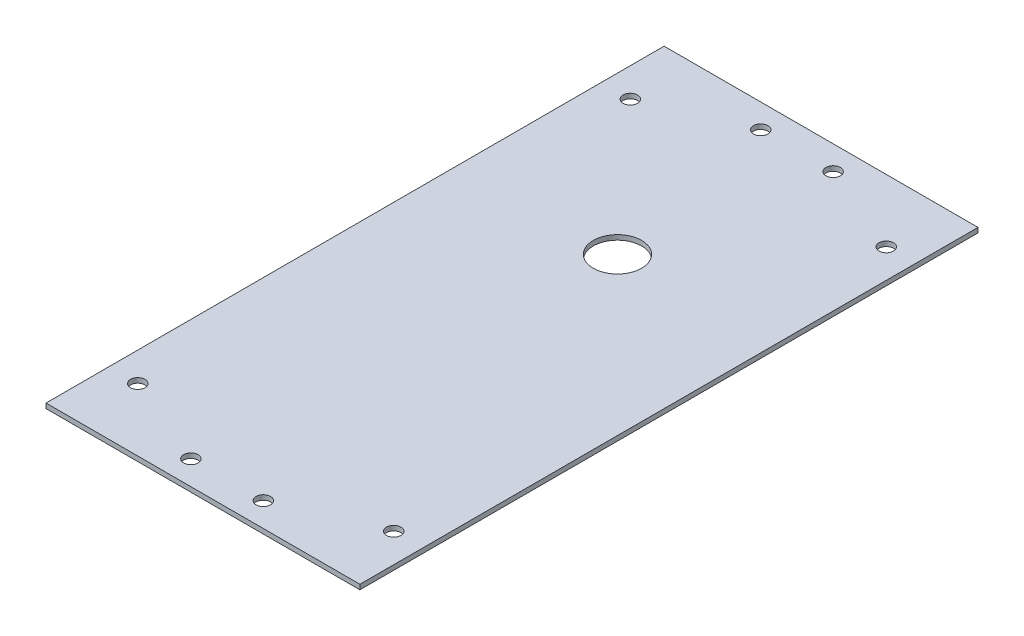
SolidWorks part; units mm, degrees
ref_plane "Спереди" through (0, 0, 0) normal (0, 0, 1) x (1, 0, 0)
ref_plane "Сверху" through (0, 0, 0) normal (0, 1, 0) x (1, 0, 0)
ref_plane "Справа" through (0, 0, 0) normal (1, 0, 0) x (0, 0, -1)
sketch "Эскиз1" plane through (0, 0, 0) normal (0, 1, 0) x (1, 0, 0)
  line L0 (-41.8585, 53.6415) -> (-41.8585, -74.3585) construction
  line L1 (-74.3585, 53.6415) -> (-9.3585, 53.6415)
  line L2 (-74.3585, 53.6415) -> (-74.3585, -74.3585)
  line L3 (-74.3585, -74.3585) -> (-9.3585, -74.3585)
  line L4 (-9.3585, 53.6415) -> (-9.3585, -74.3585)
  line L5 (-74.3585, -10.3585) -> (-9.3585, -10.3585) construction
  circle A0 centre (-68.3585, 40.6415) radius 1.5
  circle A1 centre (-15.3585, 40.6415) radius 1.5
  circle A2 centre (-15.3585, -61.3585) radius 1.5
  circle A3 centre (-68.3585, -61.3585) radius 1.5
  point P0 (0, 0)
  point P12 (-41.8585, -10.3585)
  dimension "D1" = 13
  dimension "D2" = 6
  dimension "D3" = 128
  dimension "D4" = 65
extrude "Бобышка-Вытянуть1" add sketch "Эскиз1" along normal blind 1
sketch "Эскиз2" plane through (0, 1, 0) normal (0, 1, 0) x (1, 0, 0)
  line L0 (-41.8585, 53.6415) -> (-41.8585, -74.3585) construction
  line L1 (-9.3585, 53.6415) -> (-74.3585, 53.6415) construction
  line L2 (-74.3585, -74.3585) -> (-9.3585, -74.3585) construction
  line L3 (-74.3585, -10.3585) -> (-9.3585, -10.3585) construction
  line L4 (-74.3585, 53.6415) -> (-74.3585, -74.3585) construction
  line L5 (-9.3585, -74.3585) -> (-9.3585, 53.6415) construction
  circle A0 centre (-49.3585, 48.6415) radius 1.5
  circle A1 centre (-34.3585, 48.6415) radius 1.5
  circle A2 centre (-34.3585, -69.3585) radius 1.5
  circle A3 centre (-49.3585, -69.3585) radius 1.5
  dimension "D1" = 3
  dimension "D2" = 5
  dimension "D3" = 7.5
extrude "Вырез-Вытянуть1" cut sketch "Эскиз2" against normal through all
sketch "Эскиз3" plane through (0, 1, 0) normal (0, 1, 0) x (1, 0, 0)
  line L0 (-74.3585, 53.6415) -> (-74.3585, -74.3585) construction
  line L2 (-9.3585, 53.6415) -> (-74.3585, 53.6415) construction
  circle A0 centre (-41.8585, 11.4815) radius 5
  dimension "D1" = 10
  dimension "D2" = 32.5
  dimension "D3" = 42.16
extrude "Вырез-Вытянуть2" cut sketch "Эскиз3" against normal blind 10
